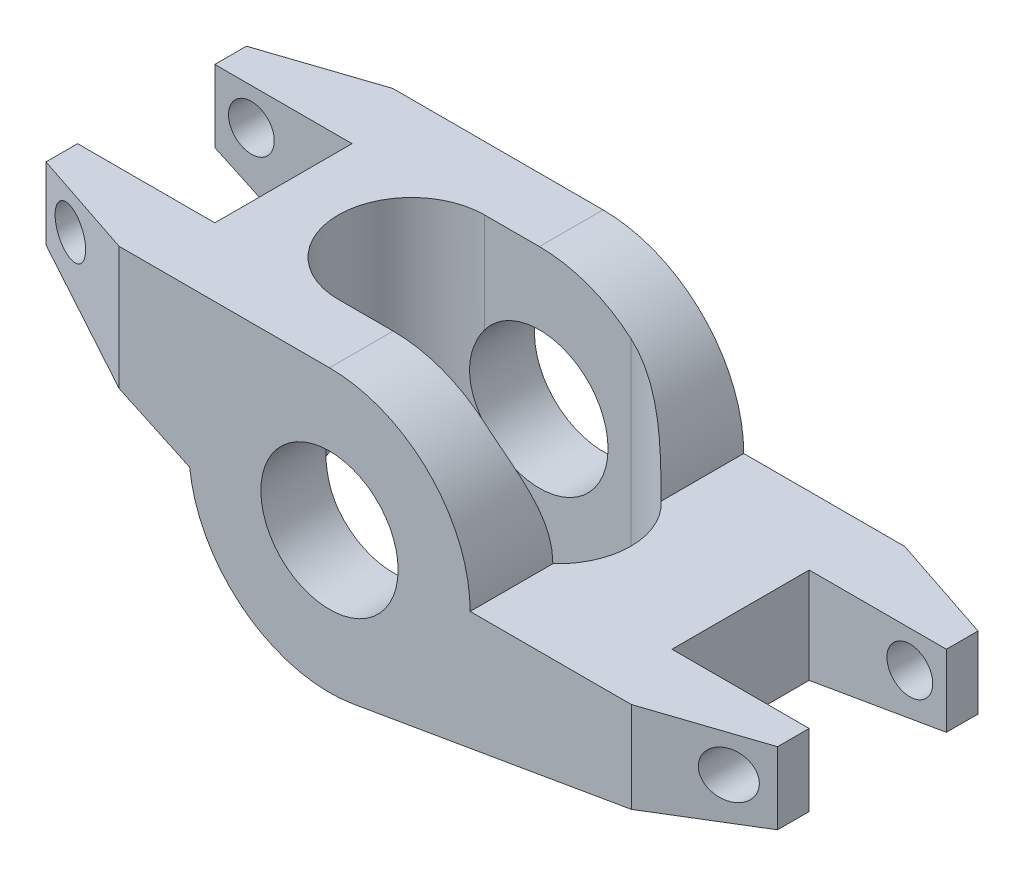
SolidWorks part; units mm, degrees
ref_plane "Front Plane" through (0, 0, 0) normal (0, 0, 1) x (1, 0, 0)
ref_plane "Top Plane" through (0, 0, 0) normal (0, 1, 0) x (1, 0, 0)
ref_plane "Right Plane" through (0, 0, 0) normal (1, 0, 0) x (0, 0, -1)
sketch "Sketch1" plane through (0, 0, 0) normal (0, 0, 1) x (1, 0, 0)
  line L0 (0, 9.77) -> (-22.23, 9.77)
  line L1 (-22.23, 9.77) -> (-22.23, 4.77)
  line L2 (-22.23, 4.77) -> (-9.7115, -1.0675)
  line L3 (28.58, 0) -> (9.77, 0)
  line L4 (28.58, 0) -> (28.58, -5)
  line L5 (28.58, -5) -> (1.6553, -9.6287)
  arc A0 (-9.7115, -1.0675) -> (1.6553, -9.6287) centre (0, 0) ccw
  circle A1 centre (0, 0) radius 4.765
  arc A2 (9.77, 0) -> (0, 9.77) centre (0, 0) ccw
  dimension "D1" = 19.54
  dimension "D2" = 9.53
  dimension "D3" = 22.23
  dimension "D4" = 5
  dimension "D5" = 25
  dimension "D6" = 28.58
extrude "Boss-Extrude1" add sketch "Sketch1" along normal mid plane 19
chamfer "Chamfer1" distance 7.62 distance2 2.54 2 edges at (28.58, -2.5, -9.5) (-22.23, 7.27, -9.5)
chamfer "Chamfer2" distance 2.54 distance2 7.62 2 edges at (28.58, -2.5, 9.5) (-22.23, 7.27, 9.5)
sketch "Sketch3" plane through (0, 9.77, 0) normal (0, 1, 0) x (1, 0, 0)
  line L0 (-22.23, -6.96) -> (-22.23, 6.96) construction
  line L1 (-22.23, -4.765) -> (-12.7, -4.765)
  line L2 (-22.23, -4.765) -> (-22.23, 4.765)
  line L3 (-22.23, 4.765) -> (-12.7, 4.765)
  line L4 (-12.7, -4.765) -> (-12.7, 4.765)
  line L5 (28.58, -6.96) -> (28.58, 6.96) construction
  line L6 (28.58, -4.765) -> (19.05, -4.765)
  line L7 (28.58, -4.765) -> (28.58, 4.765)
  line L8 (28.58, 4.765) -> (19.05, 4.765)
  line L9 (19.05, -4.765) -> (19.05, 4.765)
  point P12 (-22.23, 0)
  point P13 (19.05, 0)
  dimension "D1" = 9.53
extrude "Cut-Extrude1" cut sketch "Sketch3" against normal through all
sketch "Sketch4" plane through (0, 0, 0) normal (0, 1, 0) x (1, 0, 0)
  line L0 (-3.81, 0) -> (6.35, 0) construction
  line L1 (-3.81, 5.08) -> (6.35, 5.08)
  line L2 (-3.81, -5.08) -> (6.35, -5.08)
  line L3 (-12.7, -4.765) -> (-12.7, 4.765) construction
  arc A0 (-3.81, 5.08) -> (-3.81, -5.08) centre (-3.81, 0) ccw
  arc A1 (6.35, -5.08) -> (6.35, 5.08) centre (6.35, 0) ccw
  point P3 (1.27, 0)
  dimension "D3" = 5.08
  dimension "D1" = 8.89
  dimension "D2" = 10.16
extrude "Cut-Extrude2" cut sketch "Sketch4" against normal through all both and the other way through all
sketch "Sketch5" plane through (0, 0, 0) normal (0, 0, 1) x (1, 0, 0)
  line L0 (-22.23, 4.77) -> (-22.23, 9.77) construction
  line L1 (-22.23, 9.77) -> (-14.61, 9.77) construction
  line L2 (28.58, 0) -> (28.58, -5) construction
  line L3 (20.96, 0) -> (28.58, 0) construction
  circle A0 centre (-19.69, 7.23) radius 1.59
  circle A1 centre (26.04, -2.54) radius 1.59
  dimension "D1" = 3.18
  dimension "D2" = 2.54
  dimension "D3" = 2.54
  dimension "D4" = 2.54
  dimension "D5" = 2.54
extrude "Cut-Extrude3" cut sketch "Sketch5" against normal through all both and the other way through all
